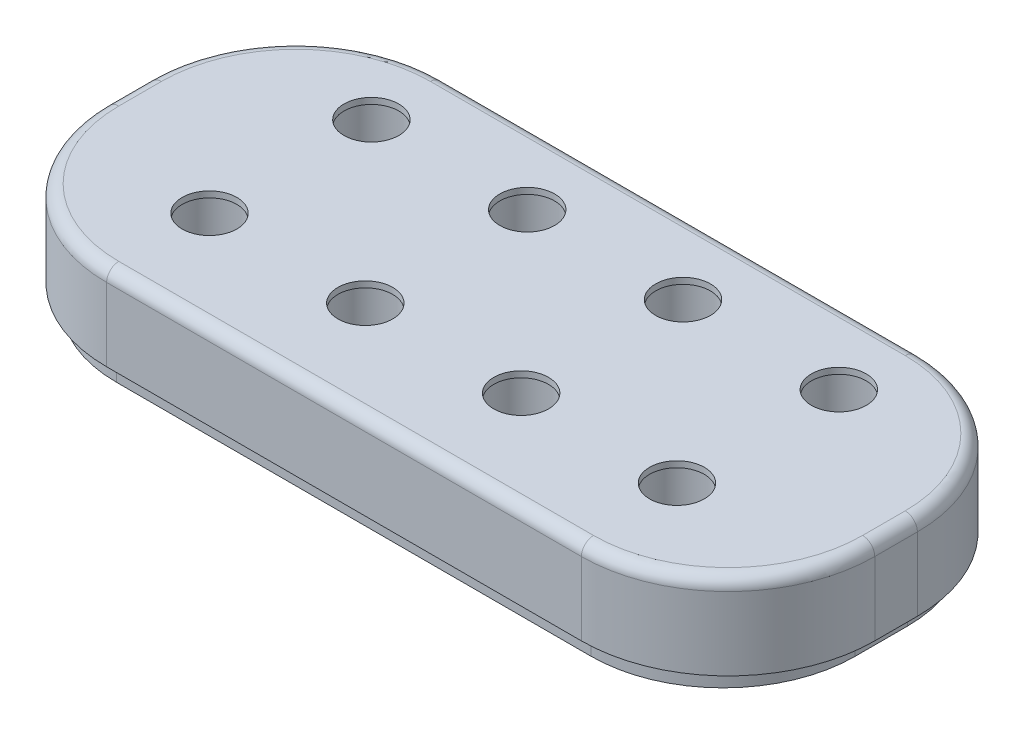
SolidWorks part; units mm, degrees
ref_plane "Front" through (0, 0, 0) normal (0, 0, 1) x (1, 0, 0)
ref_plane "Top" through (0, 0, 0) normal (0, 1, 0) x (1, 0, 0)
ref_plane "Right" through (0, 0, 0) normal (1, 0, 0) x (0, 0, -1)
sketch "Sketch1" plane through (0, 0, 0) normal (0, 1, 0) x (1, 0, 0)
  line L0 (8.0137, -3.5052) -> (-8.0137, 3.5052) construction
  line L1 (-8.0137, 3.5052) -> (8.0137, 3.5052)
  line L2 (-8.0137, 3.5052) -> (-8.0137, -3.5052)
  line L3 (-8.0137, -3.5052) -> (8.0137, -3.5052)
  line L4 (8.0137, 3.5052) -> (8.0137, -3.5052)
  dimension "D1" = 16.0274
  dimension "D2" = 7.0104
extrude "Boss-Extrude1" add sketch "Sketch1" along normal blind 1.778
sketch "Sketch3" plane through (0, 0, 0) normal (0, -1, 0) x (1, 0, 0)
  line L4 (7.7076, 3.302) -> (-7.7076, -3.302) construction
  line L5 (-7.7076, -3.302) -> (7.7076, -3.302)
  line L6 (-7.7076, -3.302) -> (-7.7076, 3.302)
  line L7 (-7.7076, 3.302) -> (7.7076, 3.302)
  line L8 (7.7076, -3.302) -> (7.7076, 3.302)
  dimension "D1" = 6.604
  dimension "D2" = 15.4153
extrude "Boss-Extrude2" add sketch "Sketch3" along normal blind 0.381
fillet "Fillet2" radius 2.7559 4 edges at (7.7076, -0.1905, 3.302) (7.7076, -0.1905, -3.302) (-7.7076, -0.1905, -3.302) (-7.7076, -0.1905, 3.302)
fillet "Fillet3" radius 3.0607 4 edges at (-8.0137, 0.889, 3.5052) (-8.0137, 0.889, -3.5052) (8.0137, 0.889, 3.5052) (8.0137, 0.889, -3.5052)
sketch "Sketch4" plane through (0, 1.778, 0) normal (0, 1, 0) x (1, 0, 0)
  line L0 (0, 0) -> (-8.8308, 0) construction
  line L1 (0, 0) -> (0, 5.661) construction
  line L2 (-1.6256, -1.4351) -> (-4.8768, -1.4351) construction
  line L3 (1.6256, -1.4351) -> (-1.6256, -1.4351) construction
  circle A0 centre (-4.8768, 1.9431) radius 0.5715
  circle A1 centre (-1.6256, 1.9431) radius 0.5715
  circle A2 centre (-4.8768, -1.4351) radius 0.5715
  circle A3 centre (-1.6256, -1.4351) radius 0.5715
  circle A4 centre (1.6256, -1.4351) radius 0.5715
  circle A5 centre (4.8768, -1.4351) radius 0.5715
  circle A6 centre (1.6256, 1.9431) radius 0.5715
  circle A7 centre (4.8768, 1.9431) radius 0.5715
  dimension "D1" = 1.143
  dimension "D2" = 1.9431
  dimension "D3" = 3.2512
  dimension "D4" = 1.4351
extrude "Cut-Extrude1" cut sketch "Sketch4" against normal through all
sketch "Sketch5" plane through (0, -0.381, 0) normal (0, 1, 0) x (1, 0, 0)
  circle A0 centre (-4.8768, -1.4351) radius 0.6985
  circle A1 centre (-4.8768, 1.9431) radius 0.6985
  circle A2 centre (-1.6256, 1.9431) radius 0.6985
  circle A3 centre (-1.6256, -1.4351) radius 0.6985
  circle A4 centre (1.6256, 1.9431) radius 0.6985
  circle A5 centre (1.6256, -1.4351) radius 0.6985
  circle A6 centre (4.8768, 1.9431) radius 0.6985
  circle A7 centre (4.8768, -1.4351) radius 0.6985
  dimension "D1" = 1.397
extrude "Cut-Extrude2" cut sketch "Sketch5" along normal blind 2.032
sketch "Sketch6" plane through (0, -0.381, 0) normal (0, 1, 0) x (1, 0, 0)
  circle A0 centre (-4.8768, 1.9431) radius 1.0414
  circle A1 centre (-4.8768, -1.4351) radius 1.0414
  circle A2 centre (-1.6256, -1.4351) radius 1.0414
  circle A3 centre (-1.6256, 1.9431) radius 1.0414
  circle A4 centre (1.6256, 1.9431) radius 1.0414
  circle A5 centre (1.6256, -1.4351) radius 1.0414
  circle A6 centre (4.8768, -1.4351) radius 1.0414
  circle A7 centre (4.8768, 1.9431) radius 1.0414
  dimension "D1" = 2.0828
extrude "Cut-Extrude3" cut sketch "Sketch6" along normal blind 0.508
sketch "Sketch7" plane through (0, -0.381, 0) normal (0, -1, 0) x (1, 0, 0)
  line L0 (7.0448, 0) -> (-7.0448, 0) construction
  circle A0 centre (0, -0.254) radius 0.1842
  dimension "D1" = 0.3683
  dimension "D2" = 0.254
extrude "Cut-Extrude4" cut sketch "Sketch7" against normal blind 0.508
fillet "Fillet4" radius 0.254 8 edges at (8.0137, 1.778, 0) (7.1172, 1.778, 2.6087) (0, 1.778, 3.5052) (-7.1172, 1.778, 2.6087) (-8.0137, 1.778, 0) (-7.1172, 1.778, -2.6087) (0, 1.778, -3.5052) (7.1172, 1.778, -2.6087)
sketch "Sketch8" plane through (0, 1.778, 0) normal (0, 1, 0) x (1, 0, 0)
  point P0 (0, 0)
  point P1 (-4.8899, 5.1388)
